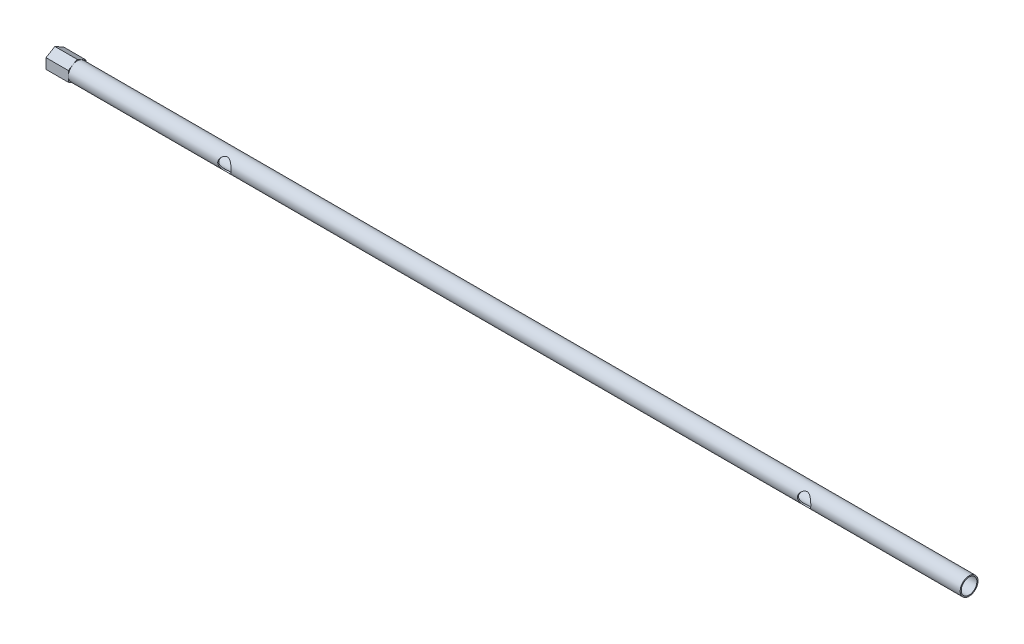
SolidWorks part; units mm, degrees
ref_plane "Front Plane" through (0, 0, 0) normal (0, 0, 1) x (1, 0, 0)
ref_plane "Top Plane" through (0, 0, 0) normal (0, 1, 0) x (1, 0, 0)
ref_plane "Right Plane" through (0, 0, 0) normal (1, 0, 0) x (0, 0, -1)
sketch "Sketch2" plane through (0, 0, 0) normal (0, 1, 0) x (1, 0, 0)
  line L0 (-100, 0) -> (100, 0)
  point P3 (0, 0)
  dimension "D1" = 200
sweep "Sweep1" add path "Sketch2" circular profile diameter 4 parameters "D3"=4
sketch "Sketch9" plane through (-100, 0, 0) normal (-1, 0, 0) x (0, 0, 1)
  line L1 (1.9883, -1.1748) -> (2.0115, 1.1345)
  line L2 (2.0115, 1.1345) -> (0.0233, 2.3093)
  line L3 (0.0233, 2.3093) -> (-1.9883, 1.1748)
  line L4 (-1.9883, 1.1748) -> (-2.0115, -1.1345)
  line L5 (-2.0115, -1.1345) -> (-0.0233, -2.3093)
  line L6 (-0.0233, -2.3093) -> (1.9883, -1.1748)
  circle A0 centre (0, 0) radius 2 construction
  circle A1 centre (0, 0) radius 2 construction
  dimension "D1" = 4
  dimension "D2" = 0.0233
extrude "Boss-Extrude1" add sketch "Sketch9" along normal blind 5
sketch "Sketch10" plane through (100, 0, 0) normal (1, 0, 0) x (0, 0, -1)
  circle A0 centre (0, 0) radius 1.75
  dimension "D1" = 3.5
extrude "Cut-Extrude1" cut sketch "Sketch10" against normal blind 200
ref_plane "Plane1" through (0, 0, 2) normal (0, 0, 1) x (1, 0, 0)
sketch "Sketch35" plane through (0, 0, 2) normal (0, 0, 1) x (1, 0, 0)
  line L0 (100, -2) -> (100, 2) construction
  line L1 (0, 33.2525) -> (0, -21.8774) construction
  circle A0 centre (65, 0) radius 1.5
  circle A1 centre (-65, 0) radius 1.5
  dimension "D1" = 3
  dimension "D2" = 35
extrude "Cut-Extrude3" cut sketch "Sketch35" against normal blind 10
